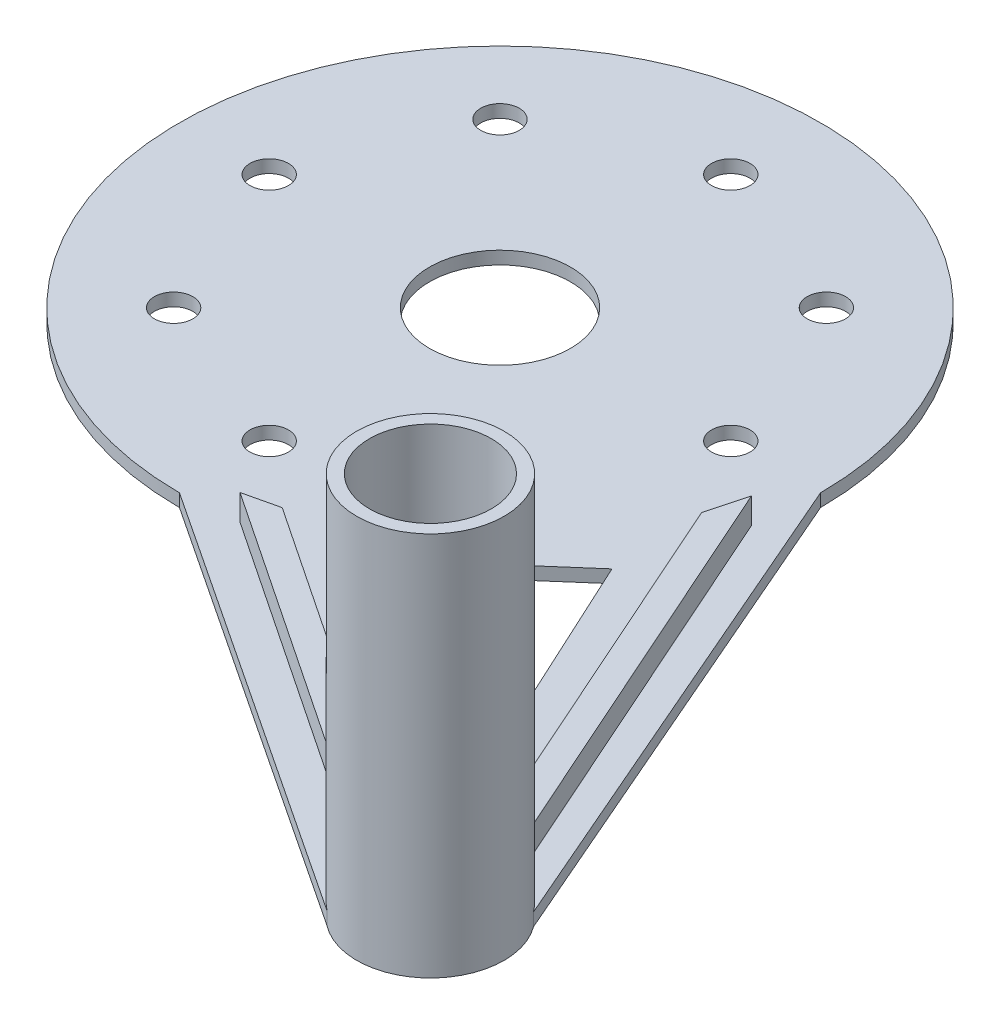
SolidWorks part; units mm, degrees
ref_plane "前视基准面" through (0, 0, 0) normal (0, 0, 1) x (1, 0, 0)
ref_plane "上视基准面" through (0, 0, 0) normal (0, 1, 0) x (1, 0, 0)
ref_plane "右视基准面" through (0, 0, 0) normal (1, 0, 0) x (0, 0, -1)
sketch "草图1" plane through (0, 0, 0) normal (0, 1, 0) x (1, 0, 0)
  circle A0 centre (37.5, -42.9273) radius 5.75
  circle A1 centre (0, 0) radius 25
  circle A2 centre (0, -18) radius 1.5
  circle A3 centre (-12.7279, -12.7279) radius 1.5
  circle A4 centre (-18, 0) radius 1.5
  circle A5 centre (-12.7279, 12.7279) radius 1.5
  circle A6 centre (0, 18) radius 1.5
  circle A7 centre (12.7279, 12.7279) radius 1.5
  circle A8 centre (18, 0) radius 1.5
  circle A9 centre (12.7279, -12.7279) radius 1.5
  circle A10 centre (0, 0) radius 5.5
  point P24 (0, 0)
  dimension "D3" = 11.5
  dimension "D4" = 50
  dimension "D6" = 3
  dimension "D1" = 11
  dimension "D2" = 57
  dimension "D5" = 18
  dimension "D7" = 8
extrude "凸台-拉伸1" add sketch "草图1" along normal blind 1
sketch "草图2" plane through (0, 0, 0) normal (0, 1, 0) x (1, 0, 0)
  line L0 (0, -25) -> (33.976, -47.4708)
  line L1 (25, 0) -> (42.1162, -39.4989)
  line L2 (25, 0) -> (15.7393, -17.7171)
  line L3 (15.7393, -17.7171) -> (0, -25)
  circle A0 centre (0, 0) radius 25 construction
  circle A1 centre (37.5, -42.9273) radius 5.75 construction
  arc A2 (42.1162, -39.4989) -> (33.976, -47.4708) centre (48.4444, -54.1026) ccw
extrude "凸台-拉伸2" add sketch "草图2" along normal blind 1
sketch "草图3" plane through (0, 0, 0) normal (0, 1, 0) x (1, 0, 0)
  circle A0 centre (37.5, -42.9273) radius 5.75
extrude "凸台-拉伸3" add sketch "草图3" along normal blind 30
sketch "草图4" plane through (0, 1, 0) normal (0, 1, 0) x (1, 0, 0)
  line L1 (16.1012, -18.4315) -> (22.0068, -13.2725)
  line L2 (22.0068, -13.2725) -> (33.7171, -38.5969)
  line L3 (16.1012, -18.4315) -> (10.1452, -23.6345)
  line L4 (10.1452, -23.6345) -> (33.7171, -38.5969)
  arc A0 (42.1162, -39.4989) -> (33.976, -47.4708) centre (37.5, -42.9273) ccw construction
extrude "切除-拉伸1" cut sketch "草图4" against normal blind 30
sketch "草图5" plane through (0, 1, 0) normal (0, 1, 0) x (1, 0, 0)
  line L0 (31.75, -42.9273) -> (4.342, -24.6201)
  line L1 (4.342, -24.6201) -> (7.0101, -23.9971)
  line L2 (7.0101, -23.9971) -> (32.1597, -40.7958)
  line L3 (32.1597, -40.7958) -> (31.75, -42.9273)
  line L4 (38.9717, -37.3688) -> (24.5153, -4.8992)
  line L5 (24.5153, -4.8992) -> (23.6945, -7.973)
  line L6 (23.6945, -7.973) -> (36.7208, -37.2303)
  line L7 (36.7208, -37.2303) -> (38.9717, -37.3688)
  circle A1 centre (37.5, -42.9273) radius 5.75 construction
  arc A2 (33.7171, -38.5969) -> (33.976, -47.4708) centre (37.5, -42.9273) ccw construction
  arc A3 (42.1162, -39.4989) -> (33.7171, -38.5969) centre (37.5, -42.9273) ccw construction
  dimension "D1" = 2
  dimension "D2" = 2
extrude "凸台-拉伸4" add sketch "草图5" along normal blind 2
sketch "草图6" plane through (0, 30, 0) normal (0, 1, 0) x (1, 0, 0)
  circle A0 centre (37.5, -42.9273) radius 4.75
  dimension "D1" = 9.5
extrude "切除-拉伸3" cut sketch "草图6" against normal blind 30
